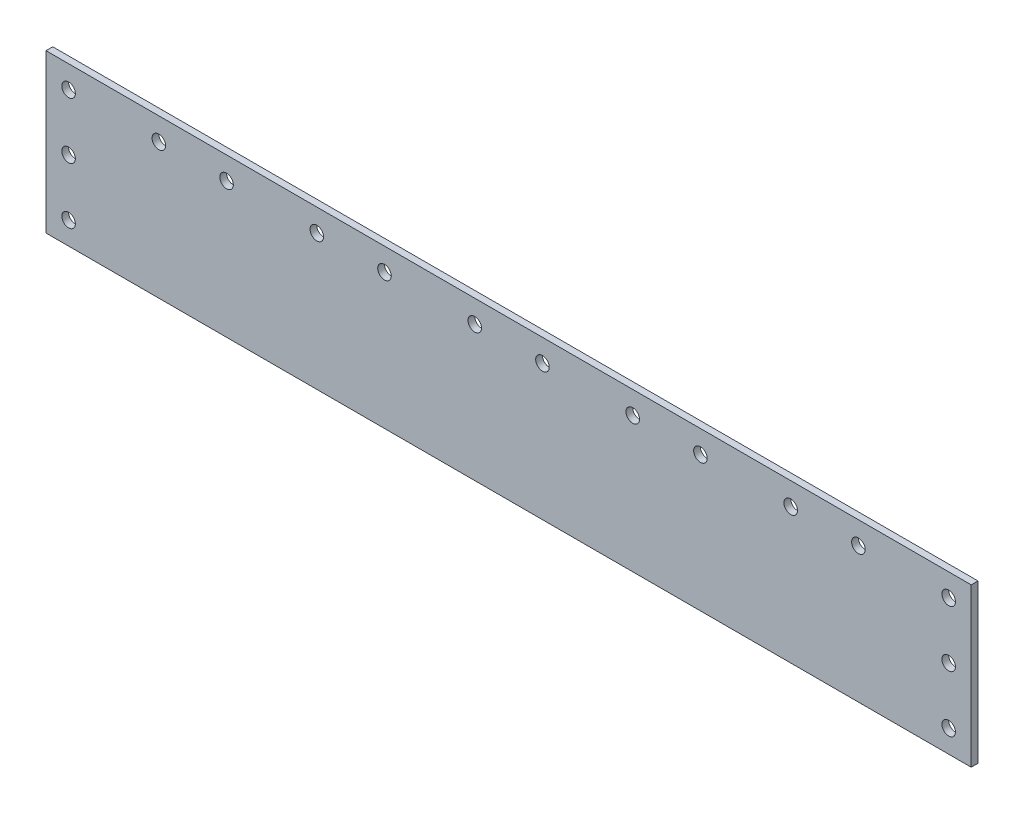
SolidWorks part; units mm, degrees
material "普通碳钢"
ref_plane "前视基准面" through (0, 0, 0) normal (0, 0, 1) x (1, 0, 0)
ref_plane "上视基准面" through (0, 0, 0) normal (0, 1, 0) x (1, 0, 0)
ref_plane "右视基准面" through (0, 0, 0) normal (1, 0, 0) x (0, 0, -1)
sketch "草图1" plane through (0, 0, 0) normal (0, 0, 1) x (1, 0, 0)
  line L0 (-15.1749, 60) -> (200.6803, 60) construction
  line L1 (0, 0) -> (410, 0)
  line L2 (0, 0) -> (0, 70)
  line L3 (0, 70) -> (410, 70)
  line L4 (410, 0) -> (410, 70)
  line L5 (0, 35) -> (410, 35) construction
  line L6 (400, 60) -> (400, 10) construction
  line L7 (10, 60) -> (10, 10) construction
  circle A0 centre (10, 60) radius 3
  circle A1 centre (50, 60) radius 3
  circle A2 centre (80, 60) radius 3
  circle A3 centre (120, 60) radius 3
  circle A4 centre (150, 60) radius 3
  circle A5 centre (190, 60) radius 3
  circle A6 centre (220, 60) radius 3
  circle A7 centre (260, 60) radius 3
  circle A8 centre (290, 60) radius 3
  circle A9 centre (330, 60) radius 3
  circle A10 centre (360, 60) radius 3
  circle A11 centre (400, 60) radius 3
  circle A12 centre (400, 10) radius 3
  circle A13 centre (10, 10) radius 3
  circle A14 centre (400, 35) radius 3
  circle A15 centre (10, 35) radius 3
  dimension "D3" = 6
  dimension "D4" = 6
  dimension "D9" = 6
  dimension "D10" = 6
  dimension "D1" = 410
  dimension "D2" = 70
  dimension "D5" = 40
  dimension "D6" = 10
  dimension "D7" = 10
  dimension "D13" = 70
  dimension "D8" = 6
extrude "凸台-拉伸1" add sketch "草图1" along normal blind 3
sketch "草图2" plane through (0, 0, 3) normal (0, 0, 1) x (1, 0, 0)
  line L1 (0, 0) -> (410, 0) construction
  spline S0 degree 3 poles (37.4563, -12.2894) (16.7382, -4.1763) (35.8525, 15.8326) (34.5731, 41.3972) (62.4568, 40.6774) (80.1677, 46.1912) (100.8825, 49.5944) (121.5829, 48.4703) (144.6192, 48.2983) (166.9339, 50.0301) (185.7531, 43.8887) (202.9992, 40.5594) (213.2744, 29.898) (217.982, 17.5964) (224.2808, 8.0681) (229.6259, 0.16) (233.5873, -14.1003) (199.6024, -4.8137) (177.9079, -9.9753) (145.6595, -8.4971) (117.9743, -10.8136) (90.4412, -9.2916) (67.5059, -11.5906) (50.9853, -10.7328) (37.4563, -12.2894) (16.7382, -4.1763) (35.8525, 15.8326) knots -0.090495 -0.057007 -0.032449 0 0.047687 0.092519 0.138286 0.188419 0.217784 0.269132 0.319364 0.364015 0.408694 0.443994 0.472409 0.49737 0.527426 0.542866 0.561115 0.600201 0.68727 0.736386 0.796706 0.864798 0.909505 0.942993 0.967551 1 1.047687 1.092519 1.138286 only from (24.3636, -4.2716) to (24.3636, -4.2716)
extrude "切除-拉伸1" [suppressed] cut sketch "草图2" against normal through all
sketch "草图3" plane through (0, 0, 3) normal (0, 0, 1) x (1, 0, 0)
  line L0 (225.7927, 80.8123) -> (-15.9059, 80.8123)
  line L1 (-15.9059, 80.8123) -> (-15.9059, -17.8947)
  line L2 (-15.9059, -17.8947) -> (254.6045, -17.8947)
  spline S0 degree 3 poles (225.7927, 80.8123) (280.9132, 48.6762) (197.3789, 12.4138) (254.6045, -17.8947) knots 0 0 0 0 1 1 1 1
extrude "切除-拉伸2" [suppressed] cut sketch "草图3" against normal through all
